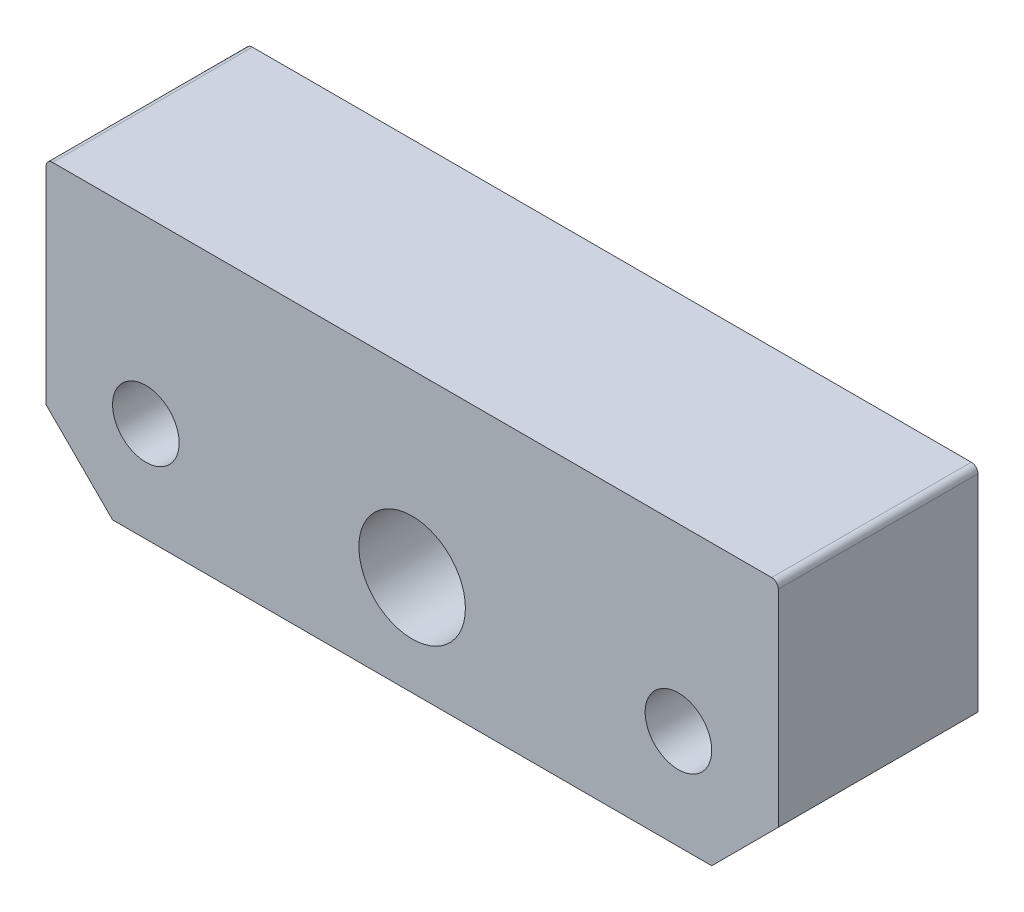
SolidWorks part; units mm, degrees
ref_plane "Alzado" through (0, 0, 0) normal (0, 0, 1) x (1, 0, 0)
ref_plane "Planta" through (0, 0, 0) normal (0, 1, 0) x (1, 0, 0)
ref_plane "Vista lateral" through (0, 0, 0) normal (1, 0, 0) x (0, 0, -1)
sketch "Croquis1" plane through (0, 0, 0) normal (0, 0, 1) x (1, 0, 0)
  line L1 (-55, -21) -> (55, -21)
  line L2 (-55, -21) -> (-55, 21)
  line L3 (-55, 21) -> (55, 21)
  line L4 (55, -21) -> (55, 21)
  line L5 (-55, -21) -> (55, 21) construction
  line L6 (-55, 21) -> (55, -21) construction
  point P0 (0, 0)
  dimension "D1" = 42
  dimension "D2" = 110
extrude "Saliente-Extruir1" add sketch "Croquis1" along normal blind 30
chamfer "Chaflán1" distance 10 angle 45 2 edges at (-55, -21, 15) (55, -21, 15)
fillet "Redondeo1" radius 1 2 edges at (-55, 21, 15) (55, 21, 15)
sketch "Croquis2" plane through (0, 0, 30) normal (0, 0, 1) x (1, 0, 0)
  line L0 (-40, -6) -> (40, -6) construction
  line L1 (54, 21) -> (-54, 21) construction
  line L2 (0, 21) -> (0, -21) construction
  line L3 (-45, -21) -> (45, -21) construction
  circle A0 centre (-40, -6) radius 5
  circle A1 centre (40, -6) radius 5
  circle A2 centre (0, -6) radius 8
  point P4 (0, -6)
  dimension "D2" = 10
  dimension "D3" = 16
  dimension "D1" = 80
  dimension "D4" = 27
extrude "Cortar-Extruir1" cut sketch "Croquis2" against normal blind 30
